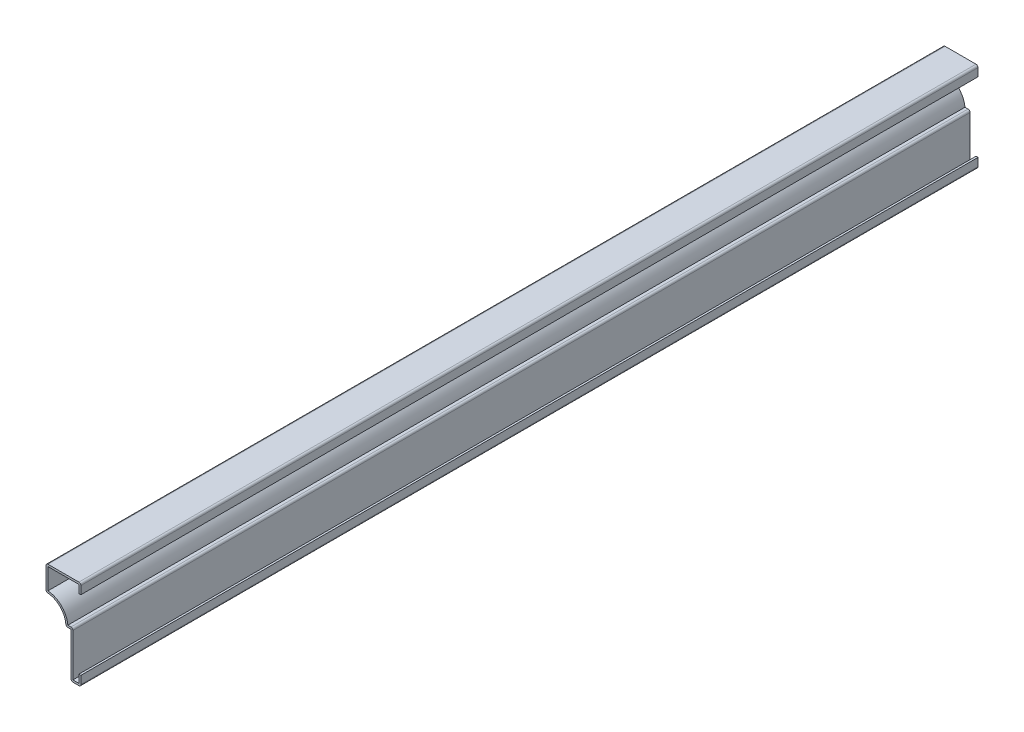
SolidWorks part; units mm, degrees
ref_plane "Front Plane" through (0, 0, 0) normal (0, 0, 1) x (1, 0, 0)
ref_plane "Top Plane" through (0, 0, 0) normal (0, 1, 0) x (1, 0, 0)
ref_plane "Right Plane" through (0, 0, 0) normal (1, 0, 0) x (0, 0, -1)
sketch "Sketch1" plane through (0, 0, 0) normal (0, 0, 1) x (1, 0, 0)
  line L0 (0, 0) -> (0, 57.15) construction
  line L1 (0, 6.35) -> (0, 0)
  line L2 (0, 0) -> (-6.35, 0)
  line L3 (-6.35, 0) -> (-6.35, 28.575)
  line L4 (-6.35, 28.575) -> (-9.525, 28.575)
  line L5 (-22.225, 41.275) -> (-22.225, 57.15)
  line L6 (-22.225, 57.15) -> (0, 57.15)
  line L7 (0, 57.15) -> (0, 50.8)
  arc A0 (-9.525, 28.575) -> (-22.225, 41.275) centre (-22.225, 28.575) ccw
extrude "Extrude-Thin1" add sketch "Sketch1" against normal blind 571.5 thin
fillet "Fillet1" radius 1.27 7 edges at (0, 0, -285.75) (-6.35, 0, -285.75) (-5.08, 29.845, -285.75) (-9.525, 28.575, -285.75) (-22.225, 41.275, -285.75) (-22.225, 57.15, -285.75) (0, 57.15, -285.75)
equation "\"D1@Extrude-Thin1\"=\"D1@Sketch1\"*10"
